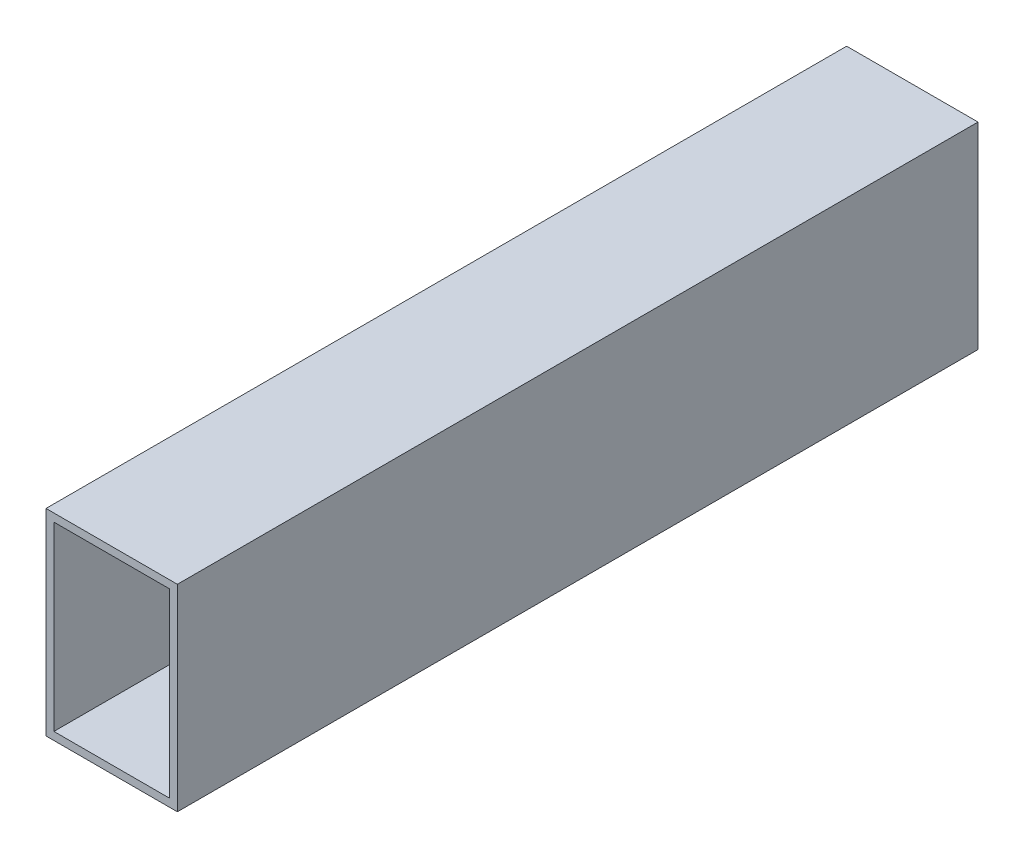
SolidWorks part; units mm, degrees
material "Plain Carbon Steel"
ref_plane "Front Plane" through (0, 0, 0) normal (0, 0, 1) x (1, 0, 0)
ref_plane "Top Plane" through (0, 0, 0) normal (0, 1, 0) x (1, 0, 0)
ref_plane "Right Plane" through (0, 0, 0) normal (1, 0, 0) x (0, 0, -1)
sketch "Sketch1" plane through (0, 0, 0) normal (0, 0, 1) x (1, 0, 0)
  line B0 (-50, -75) -> (50, -75)
  line B1 (-50, -75) -> (-50, 75)
  line B2 (50, -75) -> (50, 75)
  line B3 (-50, 75) -> (50, 75)
  line B4 (-44, -69) -> (44, -69)
  line B5 (-44, -69) -> (-44, 69)
  line B6 (44, -69) -> (44, 69)
  line B7 (-44, 69) -> (44, 69)
sketch_block_instance "15x10x6_profil-1"
sketch_block "15x10x6_profil" parameters "D1"=100, "D2"=150, "D3"=6, "D4"=6
extrude "Boss-Extrude1" add sketch "Sketch1" along normal blind 609.4381
